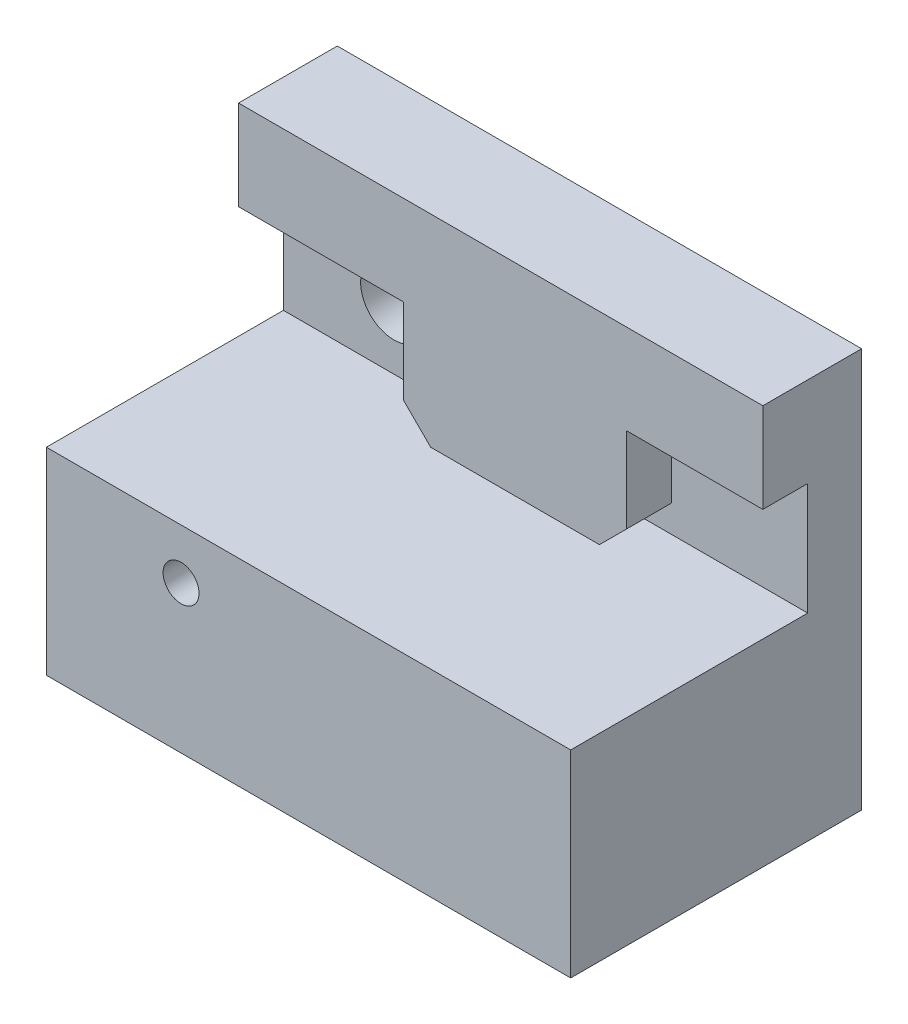
SolidWorks part; units mm, degrees
ref_plane "Front Plane" through (0, 0, 0) normal (0, 0, 1) x (1, 0, 0)
ref_plane "Top Plane" through (0, 0, 0) normal (0, 1, 0) x (1, 0, 0)
ref_plane "Right Plane" through (0, 0, 0) normal (1, 0, 0) x (0, 0, -1)
sketch "Sketch1" plane through (0, 0, 0) normal (0, 0, 1) x (1, 0, 0)
  line L0 (0, 26.5) -> (0, 16) construction
  line L1 (0, 11) -> (29.2, 11)
  line L2 (21.6, 3) -> (9.2, 3) construction
  line L3 (0, 11) -> (0, 0)
  line L4 (29.2, 26.5) -> (29.2, 16) construction
  line L5 (0, 16) -> (0, 11) construction
  line L6 (0, 16) -> (29.2, 16) construction
  line L7 (29.2, 26.5) -> (0, 26.5) construction
  line L8 (29.2, 11) -> (29.2, 0)
  line L9 (0, 21.25) -> (2.9, 21.25) construction
  line L10 (2.9, 16) -> (2.9, 26.5) construction
  line L11 (2.9, 21.25) -> (27.9, 21.25) construction
  line L12 (27.9, 16) -> (27.9, 26.5) construction
  line L13 (15.4, 21.25) -> (15.4, -12.5255) construction
  line L14 (29.2, 11) -> (29.2, 16) construction
  line L15 (0, 0) -> (29.2, 0)
  line L16 (9.2, 10.75) -> (9.2, 5.65) construction
  line L17 (9.2, 8.2) -> (7.5, 8.2) construction
  circle A0 centre (6.15, 14.5) radius 1 construction
  circle A1 centre (24.65, 14.5) radius 1 construction
  circle A2 centre (7.5, 8.2) radius 1
  circle A3 centre (23.3, 8.2) radius 1 construction
  point P20 (15.4, 3)
  dimension "D1" = 2
  dimension "D6" = 2
  dimension "D2" = 29.2
  dimension "D3" = 12
  dimension "D4" = 5.1
  dimension "D5" = 1.7
  dimension "D7" = 11
  dimension "D8" = 10.5
  dimension "D9" = 9.25
extrude "Boss-Extrude1" add sketch "Sketch1" along normal blind 13.2
sketch "Sketch6" plane through (0, 0, 0) normal (0, 0, -1) x (-1, 0, 0)
  circle A0 centre (-7.5, 8.2) radius 1.85
  dimension "D1" = 3.7
extrude "Cut-Extrude3" cut sketch "Sketch6" against normal blind 11.5
sketch "Sketch7" plane through (0, 0, 0) normal (0, 0, -1) x (-1, 0, 0)
  line L0 (-20.1, 11) -> (-10.7, 11)
  line L1 (-9.2, 12.5) -> (-9.2, 17.25)
  line L2 (-29.2, 22.25) -> (-29.2, 17.25)
  line L3 (-9.2, 17.25) -> (0, 17.25)
  line L4 (-29.2, 22.25) -> (0, 22.25)
  line L5 (-29.2, 17.25) -> (-21.6, 17.25)
  line L6 (0, 17.25) -> (0, 22.25)
  line L7 (-21.6, 17.25) -> (-21.6, 12.5)
  line L8 (-15.4, 15.2247) -> (-15.4, 11) construction
  line L9 (-10.7, 11) -> (-9.2, 12.5)
  line L10 (-20.1, 11) -> (-21.6, 12.5)
extrude "Boss-Extrude4" add sketch "Sketch7" against normal blind 2.5
sketch "Sketch8" plane through (0, 0, 0) normal (0, 0, -1) x (-1, 0, 0)
  line L0 (-29.2, 22.25) -> (0, 22.25)
  line L19 (-9.2, 8.2) -> (-7.5, 8.2) construction
  line L20 (-9.2, 10.75) -> (-9.2, 5.65) construction
  line L21 (-15.4, 21.25) -> (-15.4, -12.5255) construction
  line L22 (-27.9, 16) -> (-27.9, 26.5) construction
  line L23 (-2.9, 21.25) -> (-27.9, 21.25) construction
  line L24 (-2.9, 16) -> (-2.9, 26.5) construction
  line L25 (0, 21.25) -> (-2.9, 21.25) construction
  line L26 (0, 16) -> (-29.2, 16) construction
  line L27 (-21.6, 3) -> (-9.2, 3) construction
  line L28 (0, 10.75) -> (-29.2, 10.75) construction
  line L29 (0, 0) -> (-29.2, 0)
  line L30 (-29.2, 10.75) -> (-29.2, 16)
  line L31 (-29.2, 10.75) -> (-29.2, 0)
  line L32 (-29.2, 26.5) -> (0, 26.5) construction
  line L33 (0, 16) -> (0, 10.75)
  line L34 (-29.2, 22.25) -> (-29.2, 16)
  line L35 (0, 10.75) -> (0, 0)
  line L36 (0, 22.25) -> (0, 16)
  circle A4 centre (-23.3, 8.2) radius 1.85 construction
  circle A5 centre (-7.5, 8.2) radius 1.85
  circle A6 centre (-24.65, 14.5) radius 1.85 construction
  circle A7 centre (-6.15, 14.5) radius 1.85
  point P63 (-15.4, 3)
extrude "Boss-Extrude5" add sketch "Sketch8" along normal blind 3
